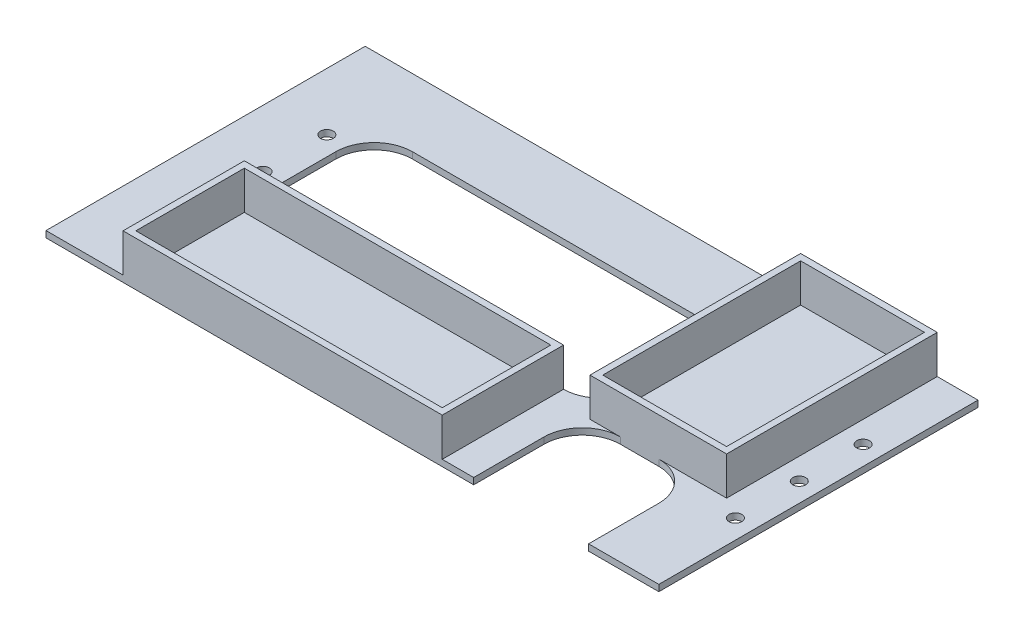
SolidWorks part; units mm, degrees
ref_plane "Front Plane" through (0, 0, 0) normal (0, 0, 1) x (1, 0, 0)
ref_plane "Top Plane" through (0, 0, 0) normal (0, 1, 0) x (1, 0, 0)
ref_plane "Right Plane" through (0, 0, 0) normal (1, 0, 0) x (0, 0, -1)
sketch "Sketch1" plane through (0, 0, 0) normal (0, 1, 0) x (1, 0, 0)
  line L1 (-225, -125) -> (225, -125)
  line L2 (-225, -125) -> (-225, 125)
  line L3 (-225, 125) -> (225, 125)
  line L4 (225, -125) -> (225, 125)
  line L5 (-225, -125) -> (225, 125) construction
  line L6 (-225, 125) -> (225, -125) construction
  point P0 (0, 0)
  dimension "D1" = 450
  dimension "D2" = 250
extrude "Boss-Extrude1" add sketch "Sketch1" along normal blind 5
sketch "Sketch2" plane through (0, 5, 0) normal (0, 1, 0) x (1, 0, 0)
  line L0 (-225, -125) -> (225, -125) construction
  line L1 (-165, 72) -> (55, 72)
  line L2 (-195, 42) -> (-195, 0)
  line L3 (-165, -30) -> (55, -30)
  line L4 (85, 42) -> (85, 0)
  line L5 (110, -40) -> (140, -40)
  line L6 (80, -70) -> (80, -125)
  line L7 (80, -125) -> (170, -125)
  line L8 (170, -70) -> (170, -125)
  line L9 (225, -125) -> (225, 125) construction
  arc A0 (-195, 0) -> (-165, -30) centre (-165, 0) ccw
  arc A1 (55, -30) -> (85, 0) centre (55, 0) ccw
  arc A2 (55, 72) -> (85, 42) centre (55, 42) cw
  arc A3 (-165, 72) -> (-195, 42) centre (-165, 42) ccw
  arc A4 (110, -40) -> (80, -70) centre (110, -70) ccw
  arc A5 (140, -40) -> (170, -70) centre (140, -70) cw
  point P12 (85, -30)
  point P17 (-195, 72)
  point P25 (80, -40)
  point P28 (170, -40)
  dimension "D5" = 30
  dimension "D9" = 30
  dimension "D1" = 72
  dimension "D2" = 30
  dimension "D3" = 195
  dimension "D4" = 85
  dimension "D6" = 85
  dimension "D7" = 90
  dimension "D8" = 55
extrude "Cut-Extrude1" cut sketch "Sketch2" against normal blind 10
sketch "Sketch3" plane through (-225, 0, 0) normal (-1, 0, 0) x (0, 0, 1)
  line L4 (-125, 0) -> (125, 0)
  line L5 (125, 0) -> (125, 5)
  line L6 (125, 5) -> (-125, 5)
  line L7 (-125, 5) -> (-125, 0)
  line L8 (-125, 0) -> (125, 0)
  line L9 (125, 0) -> (125, 5)
  line L10 (125, 5) -> (-125, 5)
  line L11 (-125, 5) -> (-125, 0)
  dimension "D1" = 0
extrude "Boss-Extrude2" add sketch "Sketch3" along normal blind 30
sketch "Sketch4" plane through (0, 5, 0) normal (0, 1, 0) x (1, 0, 0)
  line L0 (225, 0) -> (-255, 0) construction
  line L1 (225, -125) -> (225, 125) construction
  line L2 (-255, -125) -> (-255, 125) construction
  line L3 (0, 0) -> (0, 119.3802) construction
  circle A0 centre (210, 0) radius 5
  circle A1 centre (210, 50) radius 5
  circle A2 centre (210, -50) radius 5
  circle A3 centre (-210, -50) radius 5
  circle A4 centre (-210, 0) radius 5
  circle A5 centre (-210, 50) radius 5
  point P20 (0, 0)
  dimension "D1" = 10
  dimension "D2" = 100
  dimension "D3" = 50
  dimension "D4" = 15
  dimension "D5" = 15
extrude "Cut-Extrude2" cut sketch "Sketch4" against normal blind 30
sketch "Sketch5" plane through (0, 5, 0) normal (0, 1, 0) x (1, 0, 0)
  line L0 (225, 125) -> (-255, 125) construction
  line L1 (193.0769, 125) -> (86.0769, 125)
  line L2 (193.0769, 125) -> (193.0769, -40)
  line L3 (193.0769, -40) -> (86.0769, -40)
  line L4 (86.0769, 125) -> (86.0769, -40)
  line L5 (188.0769, 120) -> (188.0769, -35)
  line L6 (188.0769, -35) -> (91.0769, -35)
  line L7 (91.0769, 120) -> (91.0769, -35)
  line L8 (188.0769, 120) -> (91.0769, 120)
  line L9 (-255, -125) -> (80, -125) construction
  line L10 (55.366, -29.9978) -> (-194.634, -29.9978)
  line L11 (55.366, -29.9978) -> (55.366, -125)
  line L12 (55.366, -125) -> (-194.634, -125)
  line L13 (-194.634, -29.9978) -> (-194.634, -125)
  line L14 (50.366, -34.9978) -> (50.366, -120)
  line L15 (50.366, -120) -> (-189.634, -120)
  line L16 (-189.634, -34.9978) -> (-189.634, -120)
  line L17 (50.366, -34.9978) -> (-189.634, -34.9978)
  arc A0 (55, -30) -> (85, 0) centre (55, 0) ccw construction
  dimension "D1" = 107
  dimension "D2" = 165
  dimension "D4" = 250
  dimension "D3" = 5
  dimension "D5" = 5
extrude "Boss-Extrude3" add sketch "Sketch5" along normal blind 30
